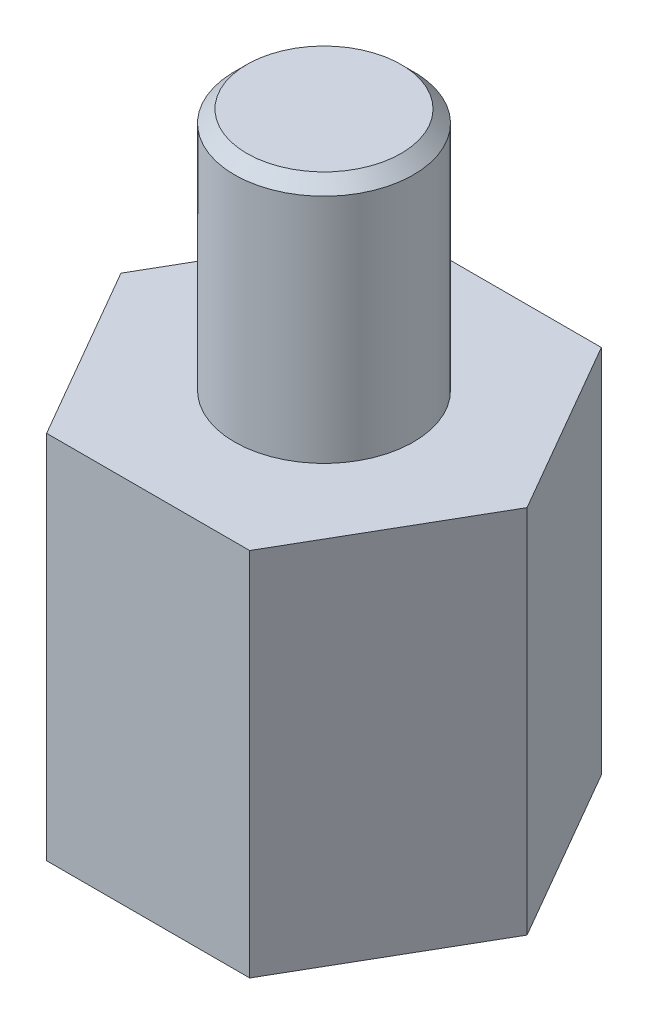
SolidWorks part; units mm, degrees
ref_plane "Front Plane" through (0, 0, 0) normal (0, 0, 1) x (1, 0, 0)
ref_plane "Top Plane" through (0, 0, 0) normal (0, 1, 0) x (1, 0, 0)
ref_plane "Right Plane" through (0, 0, 0) normal (1, 0, 0) x (0, 0, -1)
sketch "Sketch1" plane through (0, 0, 0) normal (0, 1, 0) x (1, 0, 0)
  line L1 (1.6454, -2.85) -> (3.2909, 0)
  line L2 (3.2909, 0) -> (1.6454, 2.85)
  line L3 (1.6454, 2.85) -> (-1.6454, 2.85)
  line L4 (-1.6454, 2.85) -> (-3.2909, 0)
  line L5 (-3.2909, 0) -> (-1.6454, -2.85)
  line L6 (-1.6454, -2.85) -> (1.6454, -2.85)
  circle A0 centre (0, 0) radius 2.85 construction
  circle A1 centre (0, 0) radius 1.4
  dimension "D2" = 2.8
  dimension "D1" = 5.7
extrude "Boss-Extrude1" add sketch "Sketch1" along normal blind 5
sketch "Sketch2" plane through (0, 5, 0) normal (0, 1, 0) x (1, 0, 0)
  line L6 (-1.6454, -2.85) -> (1.6454, -2.85)
  line L7 (1.6454, -2.85) -> (3.2909, 0)
  line L8 (3.2909, 0) -> (1.6454, 2.85)
  line L9 (1.6454, 2.85) -> (-1.6454, 2.85)
  line L10 (-1.6454, 2.85) -> (-3.2909, 0)
  line L11 (-3.2909, 0) -> (-1.6454, -2.85)
  line L12 (-1.6454, -2.85) -> (1.6454, -2.85)
  line L13 (1.6454, -2.85) -> (3.2909, 0)
  line L14 (3.2909, 0) -> (1.6454, 2.85)
  line L15 (1.6454, 2.85) -> (-1.6454, 2.85)
  line L16 (-1.6454, 2.85) -> (-3.2909, 0)
  line L17 (-3.2909, 0) -> (-1.6454, -2.85)
  dimension "D1" = 0
extrude "Boss-Extrude2" add sketch "Sketch2" along normal blind 1
sketch "Sketch3" plane through (0, 6, 0) normal (0, 1, 0) x (1, 0, 0)
  circle A0 centre (0, 0) radius 1.45
  dimension "D1" = 2.9
extrude "Boss-Extrude3" add sketch "Sketch3" along normal blind 3.95
chamfer "Chamfer1" distance 0.2 angle 45 1 edges at (0, 9.95, 1.45)
